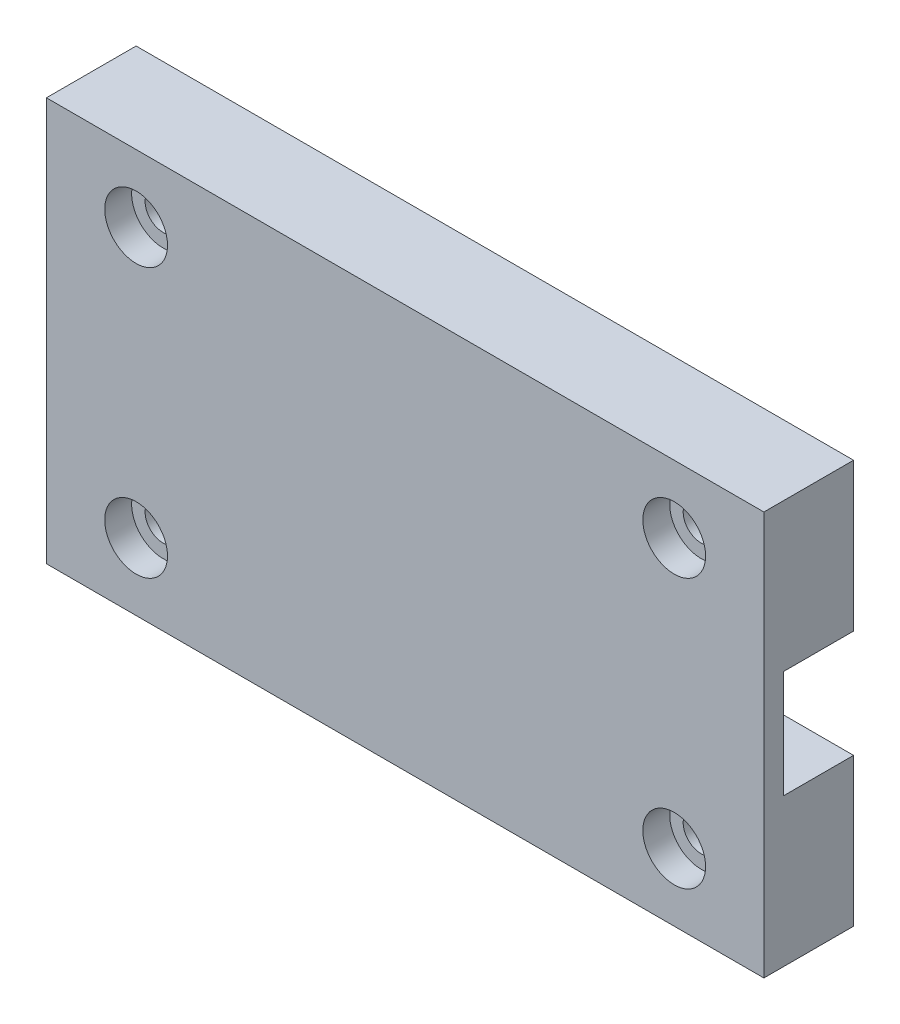
SolidWorks part; units mm, degrees
ref_plane "Front Plane" through (0, 0, 0) normal (0, 0, 1) x (1, 0, 0)
ref_plane "Top Plane" through (0, 0, 0) normal (0, 1, 0) x (1, 0, 0)
ref_plane "Right Plane" through (0, 0, 0) normal (1, 0, 0) x (0, 0, -1)
sketch "Sketch1" plane through (0, 0, 0) normal (0, 0, 1) x (1, 0, 0)
  line L1 (0, 0) -> (80, 0)
  line L2 (0, 0) -> (0, 45)
  line L3 (0, 45) -> (80, 45)
  line L4 (80, 0) -> (80, 45)
  line L5 (0, 0) -> (80, 45) construction
  line L6 (0, 45) -> (80, 0) construction
  point P4 (40, 22.5)
  dimension "D1" = 80
  dimension "D2" = 45
extrude "Boss-Extrude1" add sketch "Sketch1" along normal blind 10
sketch "Sketch2" plane through (0, 0, 0) normal (0, 0, -1) x (-1, 0, 0)
  line L0 (-80, 0) -> (-80, 45) construction
  line L1 (-80, 16.5) -> (30, 16.5)
  line L2 (-80, 16.5) -> (-80, 28.5)
  line L3 (-80, 28.5) -> (30, 28.5)
  line L4 (30, 16.5) -> (30, 28.5)
  line L5 (-80, 16.5) -> (30, 28.5) construction
  line L6 (-80, 28.5) -> (30, 16.5) construction
  line L7 (-80, 45) -> (0, 45) construction
  line L8 (0, 0) -> (-80, 0) construction
  point P4 (-25, 22.5)
  dimension "D1" = 16.5
  dimension "D2" = 16.5
  dimension "D3" = 110
extrude "Cut-Extrude1" cut sketch "Sketch2" against normal blind 7.8
sketch "Sketch4" plane through (0, 0, 10) normal (0, 0, 1) x (1, 0, 0)
  line L0 (80, 0) -> (80, 45) construction
  line L1 (70, 7.5) -> (10, 7.5) construction
  line L2 (70, 7.5) -> (70, 37.5) construction
  line L3 (70, 37.5) -> (10, 37.5) construction
  line L4 (10, 7.5) -> (10, 37.5) construction
  line L5 (70, 7.5) -> (10, 37.5) construction
  line L6 (70, 37.5) -> (10, 7.5) construction
  line L7 (80, 22.5) -> (0, 22.5) construction
  line L8 (0, 45) -> (0, 0) construction
  line L9 (40, 45) -> (40, 0) construction
  line L10 (80, 45) -> (0, 45) construction
  line L11 (0, 0) -> (80, 0) construction
  circle A0 centre (10, 37.5) radius 2
  circle A1 centre (70, 37.5) radius 2
  circle A2 centre (70, 7.5) radius 2
  circle A3 centre (10, 7.5) radius 2
  point P0 (40, 22.5)
  point P21 (0, 0)
  point P22 (0, 0)
  dimension "D4" = 4
  dimension "D1" = 30
  dimension "D2" = 60
extrude "Cut-Extrude3" cut sketch "Sketch4" against normal through all
sketch "Sketch5" plane through (0, 0, 10) normal (0, 0, 1) x (1, 0, 0)
  circle A0 centre (10, 37.5) radius 3.5
  circle A1 centre (70, 37.5) radius 3.5
  circle A2 centre (70, 7.5) radius 3.5
  circle A3 centre (10, 7.5) radius 3.5
  dimension "D1" = 7
extrude "Cut-Extrude4" cut sketch "Sketch5" against normal blind 3
